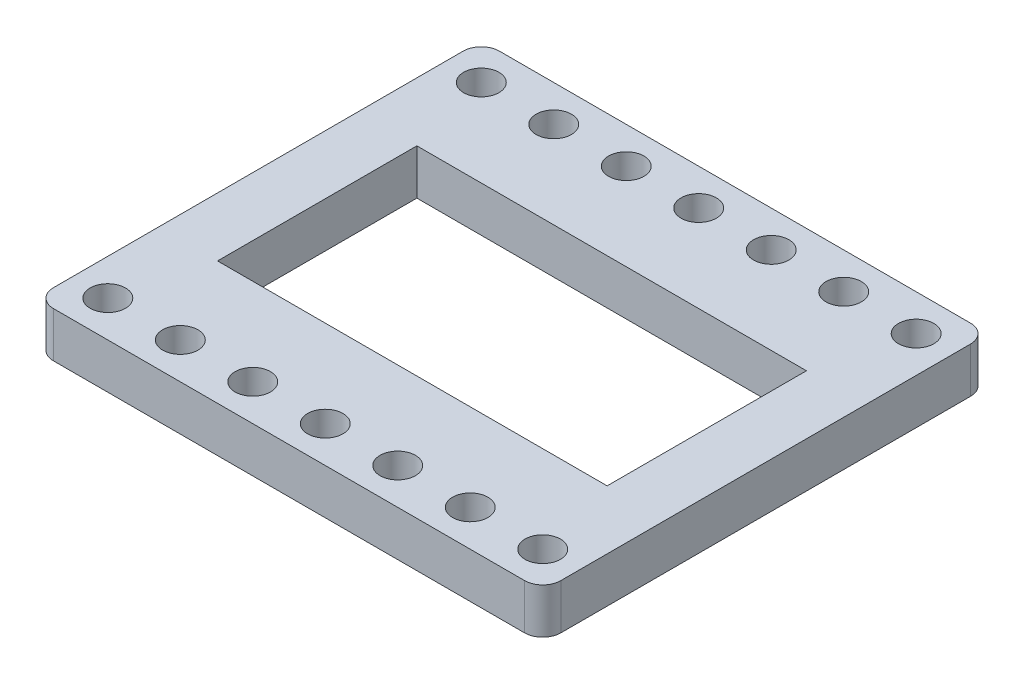
SolidWorks part; units mm, degrees
ref_plane "Front Plane" through (0, 0, 0) normal (0, 0, 1) x (1, 0, 0)
ref_plane "Top Plane" through (0, 0, 0) normal (0, 1, 0) x (1, 0, 0)
ref_plane "Right Plane" through (0, 0, 0) normal (1, 0, 0) x (0, 0, -1)
sketch "Sketch1" plane through (0, 0, 0) normal (0, 1, 0) x (1, 0, 0)
  line L1 (-54, 0) -> (-2, 0)
  line L2 (-56, -2) -> (-56, -47.22)
  line L3 (-54, -49.22) -> (-2, -49.22)
  line L4 (0, -2) -> (0, -47.22)
  arc A0 (-2, -49.22) -> (0, -47.22) centre (-2, -47.22) ccw
  arc A1 (-56, -47.22) -> (-54, -49.22) centre (-54, -47.22) ccw
  arc A2 (-54, 0) -> (-56, -2) centre (-54, -2) ccw
  arc A3 (-2, 0) -> (0, -2) centre (-2, -2) cw
  point P7 (0, -49.22)
  point P12 (-56, 0)
  point P15 (0, 0)
  dimension "D3" = 2
  dimension "D1" = 56
  dimension "D2" = 49.22
extrude "Boss-Extrude1" add sketch "Sketch1" along normal blind 5
sketch "Sketch2" plane through (0, 5, 0) normal (0, 1, 0) x (1, 0, 0)
  line L0 (-2, 0) -> (-54, 0) construction
  line L1 (0, -47.22) -> (0, -2) construction
  line L2 (-4, -4) -> (-56, -4) construction
  line L3 (-56, -2) -> (-56, -47.22) construction
  line L4 (-4, -45.22) -> (-56, -45.22) construction
  line L5 (-54, -49.22) -> (-2, -49.22) construction
  line L6 (-49.5, -24.61) -> (-6.5, -24.61) construction
  line L7 (-49.5, -13.61) -> (-6.5, -13.61)
  line L8 (-49.5, -13.61) -> (-49.5, -35.61)
  line L9 (-49.5, -35.61) -> (-6.5, -35.61)
  line L10 (-6.5, -13.61) -> (-6.5, -35.61)
  circle A0 centre (-4, -4) radius 1.95
  circle A1 centre (-12, -4) radius 1.95
  circle A2 centre (18, -4) radius 1.95
  circle A3 centre (-68, -4) radius 1.95
  circle A4 centre (-60, -4) radius 1.95
  circle A5 centre (-52, -4) radius 1.95
  circle A6 centre (-44, -4) radius 1.95
  circle A7 centre (-36, -4) radius 1.95
  circle A8 centre (-28, -4) radius 1.95
  circle A9 centre (-20, -4) radius 1.95
  circle A10 centre (-4, -45.22) radius 1.95
  circle A11 centre (-12, -45.22) radius 1.95
  circle A12 centre (18, -45.22) radius 1.95
  circle A13 centre (-68, -45.22) radius 1.95
  circle A14 centre (-60, -45.22) radius 1.95
  circle A15 centre (-52, -45.22) radius 1.95
  circle A16 centre (-44, -45.22) radius 1.95
  circle A17 centre (-36, -45.22) radius 1.95
  circle A18 centre (-28, -45.22) radius 1.95
  circle A19 centre (-20, -45.22) radius 1.95
  dimension "D1" = 3.9
  dimension "D4" = 3.9
  dimension "D7" = 3.9
  dimension "D8" = 3.9
  dimension "D9" = 3.9
  dimension "D10" = 3.9
  dimension "D11" = 3.9
  dimension "D12" = 3.9
  dimension "D13" = 3.9
  dimension "D14" = 3.9
  dimension "D22" = 3.9
  dimension "D23" = 3.9
  dimension "D25" = 3.9
  dimension "D26" = 3.9
  dimension "D27" = 3.9
  dimension "D28" = 3.9
  dimension "D29" = 3.9
  dimension "D30" = 3.9
  dimension "D31" = 3.9
  dimension "D32" = 3.9
  dimension "D3" = 4
  dimension "D5" = 8
  dimension "D6" = 4
  dimension "D15" = 8
  dimension "D16" = 8
  dimension "D17" = 8
  dimension "D18" = 8
  dimension "D19" = 8
  dimension "D20" = 8
  dimension "D21" = 8
  dimension "D24" = 8
  dimension "D33" = 8
  dimension "D34" = 8
  dimension "D35" = 8
  dimension "D36" = 8
  dimension "D37" = 8
  dimension "D38" = 8
  dimension "D39" = 8
  dimension "D40" = 4
  dimension "D41" = 4
  dimension "D42" = 22
  dimension "D43" = 6.5
  dimension "D45" = 6.5
extrude "Cut-Extrude1" cut sketch "Sketch2" against normal through all
